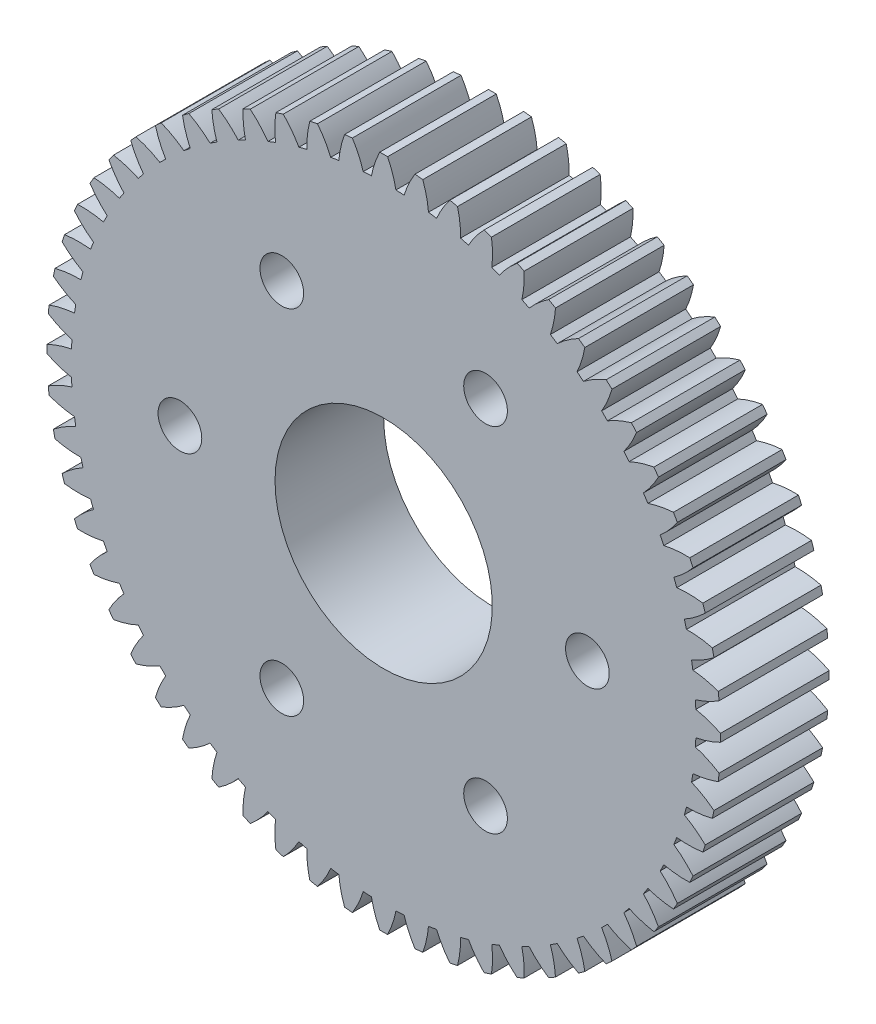
SolidWorks part; units mm, degrees
ref_plane "Front Plane" through (0, 0, 0) normal (0, 0, 1) x (1, 0, 0)
ref_plane "Top Plane" through (0, 0, 0) normal (0, 1, 0) x (1, 0, 0)
ref_plane "Right Plane" through (0, 0, 0) normal (1, 0, 0) x (0, 0, -1)
sketch "Sketch1" plane through (0, 0, 0) normal (0, 0, 1) x (1, 0, 0)
  circle A0 centre (0, 0) radius 39.3699
extrude "Boss-Extrude1" add sketch "Sketch1" against normal blind 12.7
sketch "Sketch2" plane through (0, 0, -12.7) normal (0, 0, -1) x (-1, 0, 0)
  arc A0 (8.6329, 38.4118) -> (8.9875, 35.389) centre (-2.4828, 35.5754) cw
  arc A1 (8.9875, 35.389) -> (9.9111, 35.1415) centre (0, 0) cw
  arc A2 (9.9111, 35.1415) -> (11.7296, 37.582) centre (19.9379, 29.5678) cw
  arc A3 (11.7296, 37.582) -> (8.6329, 38.4118) centre (0, 0) ccw
extrude "Cut-Extrude1" cut sketch "Sketch2" against normal through all
sketch "Sketch3" plane through (0, 0, -12.7) normal (0, 0, -1) x (-1, 0, 0)
  arc A0 (12.6007, 37.299) -> (12.6375, 34.2557) centre (1.2494, 35.6401) cw
  arc A1 (12.6375, 34.2557) -> (13.5301, 33.913) centre (0, 0) cw
  arc A2 (13.5301, 33.913) -> (15.5937, 36.1501) centre (22.9194, 27.3218) cw
  arc A3 (15.5937, 36.1501) -> (12.6007, 37.299) centre (0, 0) ccw
extrude "Cut-Extrude2" cut sketch "Sketch3" against normal through all
sketch "Sketch4" plane through (0, 0, -12.7) normal (0, 0, -1) x (-1, 0, 0)
  arc A0 (16.4305, 35.7775) -> (16.1489, 32.7471) centre (4.968, 35.3142) cw
  arc A1 (16.1489, 32.7471) -> (17.0008, 32.313) centre (0, 0) cw
  arc A2 (17.0008, 32.313) -> (19.287, 34.322) centre (25.6497, 24.7764) cw
  arc A3 (19.287, 34.322) -> (16.4305, 35.7775) centre (0, 0) ccw
extrude "Cut-Extrude3" cut sketch "Sketch4" against normal through all
sketch "Sketch5" plane through (0, 0, -12.7) normal (0, 0, -1) x (-1, 0, 0)
  arc A0 (20.0803, 33.864) -> (19.4835, 30.8796) centre (8.6321, 34.6015) cw
  arc A1 (19.4835, 30.8796) -> (20.2853, 30.3589) centre (0, 0) cw
  arc A2 (20.2853, 30.3589) -> (22.769, 32.118) centre (28.099, 21.9595) cw
  arc A3 (22.769, 32.118) -> (20.0803, 33.864) centre (0, 0) ccw
extrude "Cut-Extrude4" cut sketch "Sketch5" against normal through all
sketch "Sketch6" plane through (0, 0, -12.7) normal (0, 0, -1) x (-1, 0, 0)
  arc A0 (23.51, 31.5796) -> (22.6045, 28.6739) centre (12.2017, 33.5096) cw
  arc A1 (22.6045, 28.6739) -> (23.3476, 28.0722) centre (0, 0) cw
  arc A2 (23.3476, 28.0722) -> (26.0015, 29.562) centre (30.2405, 18.9021) cw
  arc A3 (26.0015, 29.562) -> (23.51, 31.5796) centre (0, 0) ccw
extrude "Cut-Extrude5" cut sketch "Sketch6" against normal through all
sketch "Sketch7" plane through (0, 0, -12.7) normal (0, 0, -1) x (-1, 0, 0)
  arc A0 (26.6822, 28.9491) -> (25.4779, 26.154) centre (15.6375, 32.0506) cw
  arc A1 (25.4779, 26.154) -> (26.154, 25.4779) centre (0, 0) cw
  arc A2 (26.154, 25.4779) -> (28.9491, 26.6822) centre (32.0506, 15.6375) cw
  arc A3 (28.9491, 26.6822) -> (26.6822, 28.9491) centre (0, 0) ccw
extrude "Cut-Extrude6" cut sketch "Sketch7" against normal through all
sketch "Sketch8" plane through (0, 0, -12.7) normal (0, 0, -1) x (-1, 0, 0)
  arc A0 (29.562, 26.0015) -> (28.0722, 23.3476) centre (18.9021, 30.2405) cw
  arc A1 (28.0722, 23.3476) -> (28.6739, 22.6045) centre (0, 0) cw
  arc A2 (28.6739, 22.6045) -> (31.5796, 23.51) centre (33.5096, 12.2017) cw
  arc A3 (31.5796, 23.51) -> (29.562, 26.0015) centre (0, 0) ccw
extrude "Cut-Extrude7" cut sketch "Sketch8" against normal through all
sketch "Sketch9" plane through (0, 0, -12.7) normal (0, 0, -1) x (-1, 0, 0)
  arc A0 (32.118, 22.769) -> (30.3589, 20.2853) centre (21.9595, 28.099) cw
  arc A1 (30.3589, 20.2853) -> (30.8796, 19.4835) centre (0, 0) cw
  arc A2 (30.8796, 19.4835) -> (33.864, 20.0803) centre (34.6015, 8.6321) cw
  arc A3 (33.864, 20.0803) -> (32.118, 22.769) centre (0, 0) ccw
extrude "Cut-Extrude8" cut sketch "Sketch9" against normal through all
sketch "Sketch10" plane through (0, 0, -12.7) normal (0, 0, -1) x (-1, 0, 0)
  arc A0 (34.322, 19.287) -> (32.313, 17.0008) centre (24.7764, 25.6497) cw
  arc A1 (32.313, 17.0008) -> (32.7471, 16.1489) centre (0, 0) cw
  arc A2 (32.7471, 16.1489) -> (35.7775, 16.4305) centre (35.3142, 4.968) cw
  arc A3 (35.7775, 16.4305) -> (34.322, 19.287) centre (0, 0) ccw
extrude "Cut-Extrude9" cut sketch "Sketch10" against normal through all
sketch "Sketch11" plane through (0, 0, -12.7) normal (0, 0, -1) x (-1, 0, 0)
  arc A0 (36.1501, 15.5937) -> (33.913, 13.5301) centre (27.3218, 22.9194) cw
  arc A1 (33.913, 13.5301) -> (34.2557, 12.6375) centre (0, 0) cw
  arc A2 (34.2557, 12.6375) -> (37.299, 12.6007) centre (35.6401, 1.2494) cw
  arc A3 (37.299, 12.6007) -> (36.1501, 15.5937) centre (0, 0) ccw
extrude "Cut-Extrude10" cut sketch "Sketch11" against normal through all
sketch "Sketch12" plane through (0, 0, -12.7) normal (0, 0, -1) x (-1, 0, 0)
  arc A0 (37.582, 11.7296) -> (35.1415, 9.9111) centre (29.5678, 19.9379) cw
  arc A1 (35.1415, 9.9111) -> (35.389, 8.9875) centre (0, 0) cw
  arc A2 (35.389, 8.9875) -> (38.4118, 8.6329) centre (35.5754, -2.4828) cw
  arc A3 (38.4118, 8.6329) -> (37.582, 11.7296) centre (0, 0) ccw
extrude "Cut-Extrude11" cut sketch "Sketch12" against normal through all
sketch "Sketch13" plane through (0, 0, -12.7) normal (0, 0, -1) x (-1, 0, 0)
  arc A0 (38.6022, 7.7369) -> (35.985, 6.1835) centre (31.4899, 16.738) cw
  arc A1 (35.985, 6.1835) -> (36.1346, 5.2391) centre (0, 0) cw
  arc A2 (36.1346, 5.2391) -> (39.1037, 4.5705) centre (35.121, -6.1879) cw
  arc A3 (39.1037, 4.5705) -> (38.6022, 7.7369) centre (0, 0) ccw
extrude "Cut-Extrude12" cut sketch "Sketch13" against normal through all
sketch "Sketch14" plane through (0, 0, -12.7) normal (0, 0, -1) x (-1, 0, 0)
  arc A0 (39.1995, 3.6595) -> (36.4342, 2.3881) centre (33.067, 13.3547) cw
  arc A1 (36.4342, 2.3881) -> (36.4843, 1.4334) centre (0, 0) cw
  arc A2 (36.4843, 1.4334) -> (39.3673, 0.458) centre (34.2818, -9.8251) cw
  arc A3 (39.3673, 0.458) -> (39.1995, 3.6595) centre (0, 0) ccw
extrude "Cut-Extrude13" cut sketch "Sketch14" against normal through all
sketch "Sketch15" plane through (0, 0, -12.7) normal (0, 0, -1) x (-1, 0, 0)
  arc A0 (39.3673, -0.458) -> (36.4843, -1.4334) centre (34.2818, 9.8251) cw
  arc A1 (36.4843, -1.4334) -> (36.4342, -2.3881) centre (0, 0) cw
  arc A2 (36.4342, -2.3881) -> (39.1995, -3.6595) centre (33.067, -13.3547) cw
  arc A3 (39.1995, -3.6595) -> (39.3673, -0.458) centre (0, 0) ccw
extrude "Cut-Extrude14" cut sketch "Sketch15" against normal through all
sketch "Sketch16" plane through (0, 0, -12.7) normal (0, 0, -1) x (-1, 0, 0)
  arc A0 (39.1037, -4.5705) -> (36.1346, -5.2391) centre (35.121, 6.1879) cw
  arc A1 (36.1346, -5.2391) -> (35.985, -6.1835) centre (0, 0) cw
  arc A2 (35.985, -6.1835) -> (38.6022, -7.7369) centre (31.4899, -16.738) cw
  arc A3 (38.6022, -7.7369) -> (39.1037, -4.5705) centre (0, 0) ccw
extrude "Cut-Extrude15" cut sketch "Sketch16" against normal through all
sketch "Sketch17" plane through (0, 0, -12.7) normal (0, 0, -1) x (-1, 0, 0)
  arc A0 (38.4118, -8.6329) -> (35.389, -8.9875) centre (35.5754, 2.4828) cw
  arc A1 (35.389, -8.9875) -> (35.1415, -9.9111) centre (0, 0) cw
  arc A2 (35.1415, -9.9111) -> (37.582, -11.7296) centre (29.5678, -19.9379) cw
  arc A3 (37.582, -11.7296) -> (38.4118, -8.6329) centre (0, 0) ccw
extrude "Cut-Extrude16" cut sketch "Sketch17" against normal through all
sketch "Sketch18" plane through (0, 0, -12.7) normal (0, 0, -1) x (-1, 0, 0)
  arc A0 (37.299, -12.6007) -> (34.2557, -12.6375) centre (35.6401, -1.2494) cw
  arc A1 (34.2557, -12.6375) -> (33.913, -13.5301) centre (0, 0) cw
  arc A2 (33.913, -13.5301) -> (36.1501, -15.5937) centre (27.3218, -22.9194) cw
  arc A3 (36.1501, -15.5937) -> (37.299, -12.6007) centre (0, 0) ccw
extrude "Cut-Extrude17" cut sketch "Sketch18" against normal through all
sketch "Sketch19" plane through (0, 0, -12.7) normal (0, 0, -1) x (-1, 0, 0)
  arc A0 (35.7775, -16.4305) -> (32.7471, -16.1489) centre (35.3142, -4.968) cw
  arc A1 (32.7471, -16.1489) -> (32.313, -17.0008) centre (0, 0) cw
  arc A2 (32.313, -17.0008) -> (34.322, -19.287) centre (24.7764, -25.6497) cw
  arc A3 (34.322, -19.287) -> (35.7775, -16.4305) centre (0, 0) ccw
extrude "Cut-Extrude18" cut sketch "Sketch19" against normal through all
sketch "Sketch20" plane through (0, 0, -12.7) normal (0, 0, -1) x (-1, 0, 0)
  arc A0 (33.864, -20.0803) -> (30.8796, -19.4835) centre (34.6015, -8.6321) cw
  arc A1 (30.8796, -19.4835) -> (30.3589, -20.2853) centre (0, 0) cw
  arc A2 (30.3589, -20.2853) -> (32.118, -22.769) centre (21.9595, -28.099) cw
  arc A3 (32.118, -22.769) -> (33.864, -20.0803) centre (0, 0) ccw
extrude "Cut-Extrude19" cut sketch "Sketch20" against normal through all
sketch "Sketch21" plane through (0, 0, -12.7) normal (0, 0, -1) x (-1, 0, 0)
  arc A0 (31.5796, -23.51) -> (28.6739, -22.6045) centre (33.5096, -12.2017) cw
  arc A1 (28.6739, -22.6045) -> (28.0722, -23.3476) centre (0, 0) cw
  arc A2 (28.0722, -23.3476) -> (29.562, -26.0015) centre (18.9021, -30.2405) cw
  arc A3 (29.562, -26.0015) -> (31.5796, -23.51) centre (0, 0) ccw
extrude "Cut-Extrude20" cut sketch "Sketch21" against normal through all
sketch "Sketch22" plane through (0, 0, -12.7) normal (0, 0, -1) x (-1, 0, 0)
  arc A0 (28.9491, -26.6822) -> (26.154, -25.4779) centre (32.0506, -15.6375) cw
  arc A1 (26.154, -25.4779) -> (25.4779, -26.154) centre (0, 0) cw
  arc A2 (25.4779, -26.154) -> (26.6822, -28.9491) centre (15.6375, -32.0506) cw
  arc A3 (26.6822, -28.9491) -> (28.9491, -26.6822) centre (0, 0) ccw
extrude "Cut-Extrude21" cut sketch "Sketch22" against normal through all
sketch "Sketch23" plane through (0, 0, -12.7) normal (0, 0, -1) x (-1, 0, 0)
  arc A0 (26.0015, -29.562) -> (23.3476, -28.0722) centre (30.2405, -18.9021) cw
  arc A1 (23.3476, -28.0722) -> (22.6045, -28.6739) centre (0, 0) cw
  arc A2 (22.6045, -28.6739) -> (23.51, -31.5796) centre (12.2017, -33.5096) cw
  arc A3 (23.51, -31.5796) -> (26.0015, -29.562) centre (0, 0) ccw
extrude "Cut-Extrude22" cut sketch "Sketch23" against normal through all
sketch "Sketch24" plane through (0, 0, -12.7) normal (0, 0, -1) x (-1, 0, 0)
  arc A0 (22.769, -32.118) -> (20.2853, -30.3589) centre (28.099, -21.9595) cw
  arc A1 (20.2853, -30.3589) -> (19.4835, -30.8796) centre (0, 0) cw
  arc A2 (19.4835, -30.8796) -> (20.0803, -33.864) centre (8.6321, -34.6015) cw
  arc A3 (20.0803, -33.864) -> (22.769, -32.118) centre (0, 0) ccw
extrude "Cut-Extrude23" cut sketch "Sketch24" against normal through all
sketch "Sketch25" plane through (0, 0, -12.7) normal (0, 0, -1) x (-1, 0, 0)
  arc A0 (19.287, -34.322) -> (17.0008, -32.313) centre (25.6497, -24.7764) cw
  arc A1 (17.0008, -32.313) -> (16.1489, -32.7471) centre (0, 0) cw
  arc A2 (16.1489, -32.7471) -> (16.4305, -35.7775) centre (4.968, -35.3142) cw
  arc A3 (16.4305, -35.7775) -> (19.287, -34.322) centre (0, 0) ccw
extrude "Cut-Extrude24" cut sketch "Sketch25" against normal through all
sketch "Sketch26" plane through (0, 0, -12.7) normal (0, 0, -1) x (-1, 0, 0)
  arc A0 (15.5937, -36.1501) -> (13.5301, -33.913) centre (22.9194, -27.3218) cw
  arc A1 (13.5301, -33.913) -> (12.6375, -34.2557) centre (0, 0) cw
  arc A2 (12.6375, -34.2557) -> (12.6007, -37.299) centre (1.2494, -35.6401) cw
  arc A3 (12.6007, -37.299) -> (15.5937, -36.1501) centre (0, 0) ccw
extrude "Cut-Extrude25" cut sketch "Sketch26" against normal through all
sketch "Sketch27" plane through (0, 0, -12.7) normal (0, 0, -1) x (-1, 0, 0)
  arc A0 (11.7296, -37.582) -> (9.9111, -35.1415) centre (19.9379, -29.5678) cw
  arc A1 (9.9111, -35.1415) -> (8.9875, -35.389) centre (0, 0) cw
  arc A2 (8.9875, -35.389) -> (8.6329, -38.4118) centre (-2.4828, -35.5754) cw
  arc A3 (8.6329, -38.4118) -> (11.7296, -37.582) centre (0, 0) ccw
extrude "Cut-Extrude26" cut sketch "Sketch27" against normal through all
sketch "Sketch28" plane through (0, 0, -12.7) normal (0, 0, -1) x (-1, 0, 0)
  arc A0 (7.7369, -38.6022) -> (6.1835, -35.985) centre (16.738, -31.4899) cw
  arc A1 (6.1835, -35.985) -> (5.2391, -36.1346) centre (0, 0) cw
  arc A2 (5.2391, -36.1346) -> (4.5705, -39.1037) centre (-6.1879, -35.121) cw
  arc A3 (4.5705, -39.1037) -> (7.7369, -38.6022) centre (0, 0) ccw
extrude "Cut-Extrude27" cut sketch "Sketch28" against normal through all
sketch "Sketch29" plane through (0, 0, -12.7) normal (0, 0, -1) x (-1, 0, 0)
  arc A0 (3.6595, -39.1995) -> (2.3881, -36.4342) centre (13.3547, -33.067) cw
  arc A1 (2.3881, -36.4342) -> (1.4334, -36.4843) centre (0, 0) cw
  arc A2 (1.4334, -36.4843) -> (0.458, -39.3673) centre (-9.8251, -34.2818) cw
  arc A3 (0.458, -39.3673) -> (3.6595, -39.1995) centre (0, 0) ccw
extrude "Cut-Extrude28" cut sketch "Sketch29" against normal through all
sketch "Sketch30" plane through (0, 0, -12.7) normal (0, 0, -1) x (-1, 0, 0)
  arc A0 (-0.458, -39.3673) -> (-1.4334, -36.4843) centre (9.8251, -34.2818) cw
  arc A1 (-1.4334, -36.4843) -> (-2.3881, -36.4342) centre (0, 0) cw
  arc A2 (-2.3881, -36.4342) -> (-3.6595, -39.1995) centre (-13.3547, -33.067) cw
  arc A3 (-3.6595, -39.1995) -> (-0.458, -39.3673) centre (0, 0) ccw
extrude "Cut-Extrude29" cut sketch "Sketch30" against normal through all
sketch "Sketch31" plane through (0, 0, -12.7) normal (0, 0, -1) x (-1, 0, 0)
  arc A0 (-4.5705, -39.1037) -> (-5.2391, -36.1346) centre (6.1879, -35.121) cw
  arc A1 (-5.2391, -36.1346) -> (-6.1835, -35.985) centre (0, 0) cw
  arc A2 (-6.1835, -35.985) -> (-7.7369, -38.6022) centre (-16.738, -31.4899) cw
  arc A3 (-7.7369, -38.6022) -> (-4.5705, -39.1037) centre (0, 0) ccw
extrude "Cut-Extrude30" cut sketch "Sketch31" against normal through all
sketch "Sketch32" plane through (0, 0, -12.7) normal (0, 0, -1) x (-1, 0, 0)
  arc A0 (-8.6329, -38.4118) -> (-8.9875, -35.389) centre (2.4828, -35.5754) cw
  arc A1 (-8.9875, -35.389) -> (-9.9111, -35.1415) centre (0, 0) cw
  arc A2 (-9.9111, -35.1415) -> (-11.7296, -37.582) centre (-19.9379, -29.5678) cw
  arc A3 (-11.7296, -37.582) -> (-8.6329, -38.4118) centre (0, 0) ccw
extrude "Cut-Extrude31" cut sketch "Sketch32" against normal through all
sketch "Sketch33" plane through (0, 0, -12.7) normal (0, 0, -1) x (-1, 0, 0)
  arc A0 (-12.6007, -37.299) -> (-12.6375, -34.2557) centre (-1.2494, -35.6401) cw
  arc A1 (-12.6375, -34.2557) -> (-13.5301, -33.913) centre (0, 0) cw
  arc A2 (-13.5301, -33.913) -> (-15.5937, -36.1501) centre (-22.9194, -27.3218) cw
  arc A3 (-15.5937, -36.1501) -> (-12.6007, -37.299) centre (0, 0) ccw
extrude "Cut-Extrude32" cut sketch "Sketch33" against normal through all
sketch "Sketch34" plane through (0, 0, -12.7) normal (0, 0, -1) x (-1, 0, 0)
  arc A0 (-16.4305, -35.7775) -> (-16.1489, -32.7471) centre (-4.968, -35.3142) cw
  arc A1 (-16.1489, -32.7471) -> (-17.0008, -32.313) centre (0, 0) cw
  arc A2 (-17.0008, -32.313) -> (-19.287, -34.322) centre (-25.6497, -24.7764) cw
  arc A3 (-19.287, -34.322) -> (-16.4305, -35.7775) centre (0, 0) ccw
extrude "Cut-Extrude33" cut sketch "Sketch34" against normal through all
sketch "Sketch35" plane through (0, 0, -12.7) normal (0, 0, -1) x (-1, 0, 0)
  arc A0 (-20.0803, -33.864) -> (-19.4835, -30.8796) centre (-8.6321, -34.6015) cw
  arc A1 (-19.4835, -30.8796) -> (-20.2853, -30.3589) centre (0, 0) cw
  arc A2 (-20.2853, -30.3589) -> (-22.769, -32.118) centre (-28.099, -21.9595) cw
  arc A3 (-22.769, -32.118) -> (-20.0803, -33.864) centre (0, 0) ccw
extrude "Cut-Extrude34" cut sketch "Sketch35" against normal through all
sketch "Sketch36" plane through (0, 0, -12.7) normal (0, 0, -1) x (-1, 0, 0)
  arc A0 (-23.51, -31.5796) -> (-22.6045, -28.6739) centre (-12.2017, -33.5096) cw
  arc A1 (-22.6045, -28.6739) -> (-23.3476, -28.0722) centre (0, 0) cw
  arc A2 (-23.3476, -28.0722) -> (-26.0015, -29.562) centre (-30.2405, -18.9021) cw
  arc A3 (-26.0015, -29.562) -> (-23.51, -31.5796) centre (0, 0) ccw
extrude "Cut-Extrude35" cut sketch "Sketch36" against normal through all
sketch "Sketch37" plane through (0, 0, -12.7) normal (0, 0, -1) x (-1, 0, 0)
  arc A0 (-26.6822, -28.9491) -> (-25.4779, -26.154) centre (-15.6375, -32.0506) cw
  arc A1 (-25.4779, -26.154) -> (-26.154, -25.4779) centre (0, 0) cw
  arc A2 (-26.154, -25.4779) -> (-28.9491, -26.6822) centre (-32.0506, -15.6375) cw
  arc A3 (-28.9491, -26.6822) -> (-26.6822, -28.9491) centre (0, 0) ccw
extrude "Cut-Extrude36" cut sketch "Sketch37" against normal through all
sketch "Sketch38" plane through (0, 0, -12.7) normal (0, 0, -1) x (-1, 0, 0)
  arc A0 (-29.562, -26.0015) -> (-28.0722, -23.3476) centre (-18.9021, -30.2405) cw
  arc A1 (-28.0722, -23.3476) -> (-28.6739, -22.6045) centre (0, 0) cw
  arc A2 (-28.6739, -22.6045) -> (-31.5796, -23.51) centre (-33.5096, -12.2017) cw
  arc A3 (-31.5796, -23.51) -> (-29.562, -26.0015) centre (0, 0) ccw
extrude "Cut-Extrude37" cut sketch "Sketch38" against normal through all
sketch "Sketch39" plane through (0, 0, -12.7) normal (0, 0, -1) x (-1, 0, 0)
  arc A0 (-32.118, -22.769) -> (-30.3589, -20.2853) centre (-21.9595, -28.099) cw
  arc A1 (-30.3589, -20.2853) -> (-30.8796, -19.4835) centre (0, 0) cw
  arc A2 (-30.8796, -19.4835) -> (-33.864, -20.0803) centre (-34.6015, -8.6321) cw
  arc A3 (-33.864, -20.0803) -> (-32.118, -22.769) centre (0, 0) ccw
extrude "Cut-Extrude38" cut sketch "Sketch39" against normal through all
sketch "Sketch40" plane through (0, 0, -12.7) normal (0, 0, -1) x (-1, 0, 0)
  arc A0 (-34.322, -19.287) -> (-32.313, -17.0008) centre (-24.7764, -25.6497) cw
  arc A1 (-32.313, -17.0008) -> (-32.7471, -16.1489) centre (0, 0) cw
  arc A2 (-32.7471, -16.1489) -> (-35.7775, -16.4305) centre (-35.3142, -4.968) cw
  arc A3 (-35.7775, -16.4305) -> (-34.322, -19.287) centre (0, 0) ccw
extrude "Cut-Extrude39" cut sketch "Sketch40" against normal through all
sketch "Sketch41" plane through (0, 0, -12.7) normal (0, 0, -1) x (-1, 0, 0)
  arc A0 (-36.1501, -15.5937) -> (-33.913, -13.5301) centre (-27.3218, -22.9194) cw
  arc A1 (-33.913, -13.5301) -> (-34.2557, -12.6375) centre (0, 0) cw
  arc A2 (-34.2557, -12.6375) -> (-37.299, -12.6007) centre (-35.6401, -1.2494) cw
  arc A3 (-37.299, -12.6007) -> (-36.1501, -15.5937) centre (0, 0) ccw
extrude "Cut-Extrude40" cut sketch "Sketch41" against normal through all
sketch "Sketch42" plane through (0, 0, -12.7) normal (0, 0, -1) x (-1, 0, 0)
  arc A0 (-37.582, -11.7296) -> (-35.1415, -9.9111) centre (-29.5678, -19.9379) cw
  arc A1 (-35.1415, -9.9111) -> (-35.389, -8.9875) centre (0, 0) cw
  arc A2 (-35.389, -8.9875) -> (-38.4118, -8.6329) centre (-35.5754, 2.4828) cw
  arc A3 (-38.4118, -8.6329) -> (-37.582, -11.7296) centre (0, 0) ccw
extrude "Cut-Extrude41" cut sketch "Sketch42" against normal through all
sketch "Sketch43" plane through (0, 0, -12.7) normal (0, 0, -1) x (-1, 0, 0)
  arc A0 (-38.6022, -7.7369) -> (-35.985, -6.1835) centre (-31.4899, -16.738) cw
  arc A1 (-35.985, -6.1835) -> (-36.1346, -5.2391) centre (0, 0) cw
  arc A2 (-36.1346, -5.2391) -> (-39.1037, -4.5705) centre (-35.121, 6.1879) cw
  arc A3 (-39.1037, -4.5705) -> (-38.6022, -7.7369) centre (0, 0) ccw
extrude "Cut-Extrude42" cut sketch "Sketch43" against normal through all
sketch "Sketch44" plane through (0, 0, -12.7) normal (0, 0, -1) x (-1, 0, 0)
  arc A0 (-39.1995, -3.6595) -> (-36.4342, -2.3881) centre (-33.067, -13.3547) cw
  arc A1 (-36.4342, -2.3881) -> (-36.4843, -1.4334) centre (0, 0) cw
  arc A2 (-36.4843, -1.4334) -> (-39.3673, -0.458) centre (-34.2818, 9.8251) cw
  arc A3 (-39.3673, -0.458) -> (-39.1995, -3.6595) centre (0, 0) ccw
extrude "Cut-Extrude43" cut sketch "Sketch44" against normal through all
sketch "Sketch45" plane through (0, 0, -12.7) normal (0, 0, -1) x (-1, 0, 0)
  arc A0 (-39.3673, 0.458) -> (-36.4843, 1.4334) centre (-34.2818, -9.8251) cw
  arc A1 (-36.4843, 1.4334) -> (-36.4342, 2.3881) centre (0, 0) cw
  arc A2 (-36.4342, 2.3881) -> (-39.1995, 3.6595) centre (-33.067, 13.3547) cw
  arc A3 (-39.1995, 3.6595) -> (-39.3673, 0.458) centre (0, 0) ccw
extrude "Cut-Extrude44" cut sketch "Sketch45" against normal through all
sketch "Sketch46" plane through (0, 0, -12.7) normal (0, 0, -1) x (-1, 0, 0)
  arc A0 (-39.1037, 4.5705) -> (-36.1346, 5.2391) centre (-35.121, -6.1879) cw
  arc A1 (-36.1346, 5.2391) -> (-35.985, 6.1835) centre (0, 0) cw
  arc A2 (-35.985, 6.1835) -> (-38.6022, 7.7369) centre (-31.4899, 16.738) cw
  arc A3 (-38.6022, 7.7369) -> (-39.1037, 4.5705) centre (0, 0) ccw
extrude "Cut-Extrude45" cut sketch "Sketch46" against normal through all
sketch "Sketch47" plane through (0, 0, -12.7) normal (0, 0, -1) x (-1, 0, 0)
  arc A0 (-38.4118, 8.6329) -> (-35.389, 8.9875) centre (-35.5754, -2.4828) cw
  arc A1 (-35.389, 8.9875) -> (-35.1415, 9.9111) centre (0, 0) cw
  arc A2 (-35.1415, 9.9111) -> (-37.582, 11.7296) centre (-29.5678, 19.9379) cw
  arc A3 (-37.582, 11.7296) -> (-38.4118, 8.6329) centre (0, 0) ccw
extrude "Cut-Extrude46" cut sketch "Sketch47" against normal through all
sketch "Sketch48" plane through (0, 0, -12.7) normal (0, 0, -1) x (-1, 0, 0)
  arc A0 (-37.299, 12.6007) -> (-34.2557, 12.6375) centre (-35.6401, 1.2494) cw
  arc A1 (-34.2557, 12.6375) -> (-33.913, 13.5301) centre (0, 0) cw
  arc A2 (-33.913, 13.5301) -> (-36.1501, 15.5937) centre (-27.3218, 22.9194) cw
  arc A3 (-36.1501, 15.5937) -> (-37.299, 12.6007) centre (0, 0) ccw
extrude "Cut-Extrude47" cut sketch "Sketch48" against normal through all
sketch "Sketch49" plane through (0, 0, -12.7) normal (0, 0, -1) x (-1, 0, 0)
  arc A0 (-35.7775, 16.4305) -> (-32.7471, 16.1489) centre (-35.3142, 4.968) cw
  arc A1 (-32.7471, 16.1489) -> (-32.313, 17.0008) centre (0, 0) cw
  arc A2 (-32.313, 17.0008) -> (-34.322, 19.287) centre (-24.7764, 25.6497) cw
  arc A3 (-34.322, 19.287) -> (-35.7775, 16.4305) centre (0, 0) ccw
extrude "Cut-Extrude48" cut sketch "Sketch49" against normal through all
sketch "Sketch50" plane through (0, 0, -12.7) normal (0, 0, -1) x (-1, 0, 0)
  arc A0 (-33.864, 20.0803) -> (-30.8796, 19.4835) centre (-34.6015, 8.6321) cw
  arc A1 (-30.8796, 19.4835) -> (-30.3589, 20.2853) centre (0, 0) cw
  arc A2 (-30.3589, 20.2853) -> (-32.118, 22.769) centre (-21.9595, 28.099) cw
  arc A3 (-32.118, 22.769) -> (-33.864, 20.0803) centre (0, 0) ccw
extrude "Cut-Extrude49" cut sketch "Sketch50" against normal through all
sketch "Sketch51" plane through (0, 0, -12.7) normal (0, 0, -1) x (-1, 0, 0)
  arc A0 (-31.5796, 23.51) -> (-28.6739, 22.6045) centre (-33.5096, 12.2017) cw
  arc A1 (-28.6739, 22.6045) -> (-28.0722, 23.3476) centre (0, 0) cw
  arc A2 (-28.0722, 23.3476) -> (-29.562, 26.0015) centre (-18.9021, 30.2405) cw
  arc A3 (-29.562, 26.0015) -> (-31.5796, 23.51) centre (0, 0) ccw
extrude "Cut-Extrude50" cut sketch "Sketch51" against normal through all
sketch "Sketch52" plane through (0, 0, -12.7) normal (0, 0, -1) x (-1, 0, 0)
  arc A0 (-28.9491, 26.6822) -> (-26.154, 25.4779) centre (-32.0506, 15.6375) cw
  arc A1 (-26.154, 25.4779) -> (-25.4779, 26.154) centre (0, 0) cw
  arc A2 (-25.4779, 26.154) -> (-26.6822, 28.9491) centre (-15.6375, 32.0506) cw
  arc A3 (-26.6822, 28.9491) -> (-28.9491, 26.6822) centre (0, 0) ccw
extrude "Cut-Extrude51" cut sketch "Sketch52" against normal through all
sketch "Sketch53" plane through (0, 0, -12.7) normal (0, 0, -1) x (-1, 0, 0)
  arc A0 (-26.0015, 29.562) -> (-23.3476, 28.0722) centre (-30.2405, 18.9021) cw
  arc A1 (-23.3476, 28.0722) -> (-22.6045, 28.6739) centre (0, 0) cw
  arc A2 (-22.6045, 28.6739) -> (-23.51, 31.5796) centre (-12.2017, 33.5096) cw
  arc A3 (-23.51, 31.5796) -> (-26.0015, 29.562) centre (0, 0) ccw
extrude "Cut-Extrude52" cut sketch "Sketch53" against normal through all
sketch "Sketch54" plane through (0, 0, -12.7) normal (0, 0, -1) x (-1, 0, 0)
  arc A0 (-22.769, 32.118) -> (-20.2853, 30.3589) centre (-28.099, 21.9595) cw
  arc A1 (-20.2853, 30.3589) -> (-19.4835, 30.8796) centre (0, 0) cw
  arc A2 (-19.4835, 30.8796) -> (-20.0803, 33.864) centre (-8.6321, 34.6015) cw
  arc A3 (-20.0803, 33.864) -> (-22.769, 32.118) centre (0, 0) ccw
extrude "Cut-Extrude53" cut sketch "Sketch54" against normal through all
sketch "Sketch55" plane through (0, 0, -12.7) normal (0, 0, -1) x (-1, 0, 0)
  arc A0 (-19.287, 34.322) -> (-17.0008, 32.313) centre (-25.6497, 24.7764) cw
  arc A1 (-17.0008, 32.313) -> (-16.1489, 32.7471) centre (0, 0) cw
  arc A2 (-16.1489, 32.7471) -> (-16.4305, 35.7775) centre (-4.968, 35.3142) cw
  arc A3 (-16.4305, 35.7775) -> (-19.287, 34.322) centre (0, 0) ccw
extrude "Cut-Extrude54" cut sketch "Sketch55" against normal through all
sketch "Sketch56" plane through (0, 0, -12.7) normal (0, 0, -1) x (-1, 0, 0)
  arc A0 (-15.5937, 36.1501) -> (-13.5301, 33.913) centre (-22.9194, 27.3218) cw
  arc A1 (-13.5301, 33.913) -> (-12.6375, 34.2557) centre (0, 0) cw
  arc A2 (-12.6375, 34.2557) -> (-12.6007, 37.299) centre (-1.2494, 35.6401) cw
  arc A3 (-12.6007, 37.299) -> (-15.5937, 36.1501) centre (0, 0) ccw
extrude "Cut-Extrude55" cut sketch "Sketch56" against normal through all
sketch "Sketch57" plane through (0, 0, -12.7) normal (0, 0, -1) x (-1, 0, 0)
  arc A0 (-11.7296, 37.582) -> (-9.9111, 35.1415) centre (-19.9379, 29.5678) cw
  arc A1 (-9.9111, 35.1415) -> (-8.9875, 35.389) centre (0, 0) cw
  arc A2 (-8.9875, 35.389) -> (-8.6329, 38.4118) centre (2.4828, 35.5754) cw
  arc A3 (-8.6329, 38.4118) -> (-11.7296, 37.582) centre (0, 0) ccw
extrude "Cut-Extrude56" cut sketch "Sketch57" against normal through all
sketch "Sketch58" plane through (0, 0, -12.7) normal (0, 0, -1) x (-1, 0, 0)
  arc A0 (-7.7369, 38.6022) -> (-6.1835, 35.985) centre (-16.738, 31.4899) cw
  arc A1 (-6.1835, 35.985) -> (-5.2391, 36.1346) centre (0, 0) cw
  arc A2 (-5.2391, 36.1346) -> (-4.5705, 39.1037) centre (6.1879, 35.121) cw
  arc A3 (-4.5705, 39.1037) -> (-7.7369, 38.6022) centre (0, 0) ccw
extrude "Cut-Extrude57" cut sketch "Sketch58" against normal through all
sketch "Sketch59" plane through (0, 0, -12.7) normal (0, 0, -1) x (-1, 0, 0)
  arc A0 (-3.6595, 39.1995) -> (-2.3881, 36.4342) centre (-13.3547, 33.067) cw
  arc A1 (-2.3881, 36.4342) -> (-1.4334, 36.4843) centre (0, 0) cw
  arc A2 (-1.4334, 36.4843) -> (-0.458, 39.3673) centre (9.8251, 34.2818) cw
  arc A3 (-0.458, 39.3673) -> (-3.6595, 39.1995) centre (0, 0) ccw
extrude "Cut-Extrude58" cut sketch "Sketch59" against normal through all
sketch "Sketch60" plane through (0, 0, -12.7) normal (0, 0, -1) x (-1, 0, 0)
  arc A0 (0.458, 39.3673) -> (1.4334, 36.4843) centre (-9.8251, 34.2818) cw
  arc A1 (1.4334, 36.4843) -> (2.3881, 36.4342) centre (0, 0) cw
  arc A2 (2.3881, 36.4342) -> (3.6595, 39.1995) centre (13.3547, 33.067) cw
  arc A3 (3.6595, 39.1995) -> (0.458, 39.3673) centre (0, 0) ccw
extrude "Cut-Extrude59" cut sketch "Sketch60" against normal through all
sketch "Sketch61" plane through (0, 0, -12.7) normal (0, 0, -1) x (-1, 0, 0)
  arc A0 (4.5705, 39.1037) -> (5.2391, 36.1346) centre (-6.1879, 35.121) cw
  arc A1 (5.2391, 36.1346) -> (6.1835, 35.985) centre (0, 0) cw
  arc A2 (6.1835, 35.985) -> (7.7369, 38.6022) centre (16.738, 31.4899) cw
  arc A3 (7.7369, 38.6022) -> (4.5705, 39.1037) centre (0, 0) ccw
extrude "Cut-Extrude60" cut sketch "Sketch61" against normal through all
hole_wizard "Hole1" positions "Sketch64" profile "Sketch63" legacy
sketch "Sketch64" plane through (0, 0, -12.7) normal (0, 0, -1) x (-1, 0, 0)
  point P0 (0, 0)
sketch "Sketch63" plane through (0, 0, -12.7) normal (1, 0, 0) x (0, 1, 0)
  line L0 (0, 0) -> (0, 12.7)
  line L1 (0, 12.7) -> (12.7, 12.7)
  line L2 (12.7, 12.7) -> (12.7, 0)
  line L3 (12.7, 0) -> (0, 0)
  line L4 (0, 110) -> (0, -10) construction
  dimension "Diameter" = 25.4
  dimension "Depth" = 12.7
hole_wizard "#10 Clearance Hole1" positions "Sketch65" profile "Sketch66" hole size "#10" standard "Ansi Inch" end condition through all
sketch "Sketch65" plane through (5.8198, 20.6554, 25.4) normal (0, 0, 1) x (1, 0, 0)
  point P0 (-17.726, -0.0332)
  point P1 (6.0865, -0.0332)
  point P2 (17.9927, -20.6554)
  point P3 (6.0865, -41.2777)
  point P4 (-17.726, -41.2777)
  point P5 (-29.6323, -20.6554)
sketch "Sketch66" plane through (-11.9062, 20.6222, 25.4) normal (1, 0, 0) x (0, -1, 0)
  line L0 (0, 0) -> (0, 38.1)
  line L1 (0, 38.1) -> (2.5527, 38.1)
  line L2 (2.5527, 38.1) -> (2.5527, 0)
  line L3 (2.5527, 0) -> (0, 0)
  line L4 (0, -6.35) -> (0, 107.95) construction
  dimension "Thru Hole Dia." = 5.1054
  dimension "Thru Hole Depth" = 38.1
